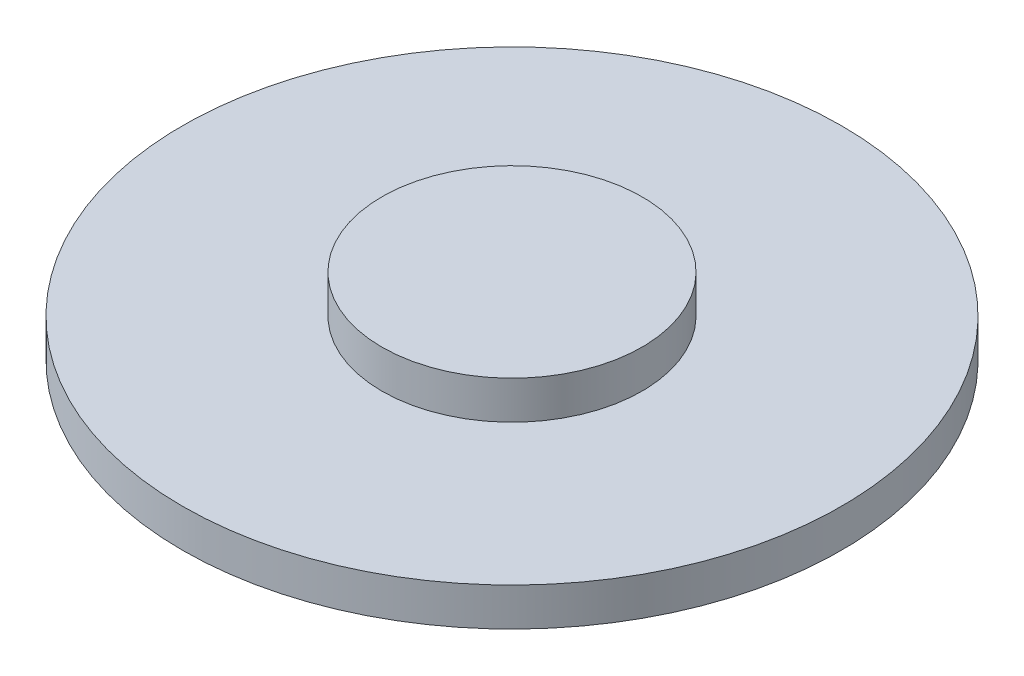
SolidWorks part; units mm, degrees
material "A-Glass Fiber"
ref_plane "Front Plane" through (0, 0, 0) normal (0, 0, 1) x (1, 0, 0)
ref_plane "Top Plane" through (0, 0, 0) normal (0, 1, 0) x (1, 0, 0)
ref_plane "Right Plane" through (0, 0, 0) normal (1, 0, 0) x (0, 0, -1)
sketch "Sketch1" plane through (0, 0, 0) normal (0, 1, 0) x (1, 0, 0)
  circle A0 centre (0, 0) radius 10.0965
  dimension "D1" = 20.193
extrude "Boss-Extrude1" add sketch "Sketch1" along normal blind 1.1684
sketch "Sketch2" plane through (0, 1.1684, 0) normal (0, 1, 0) x (1, 0, 0)
  circle A0 centre (0, 0) radius 3.9878
  dimension "D1" = 7.9756
extrude "Boss-Extrude2" add sketch "Sketch2" along normal blind 1.1684
